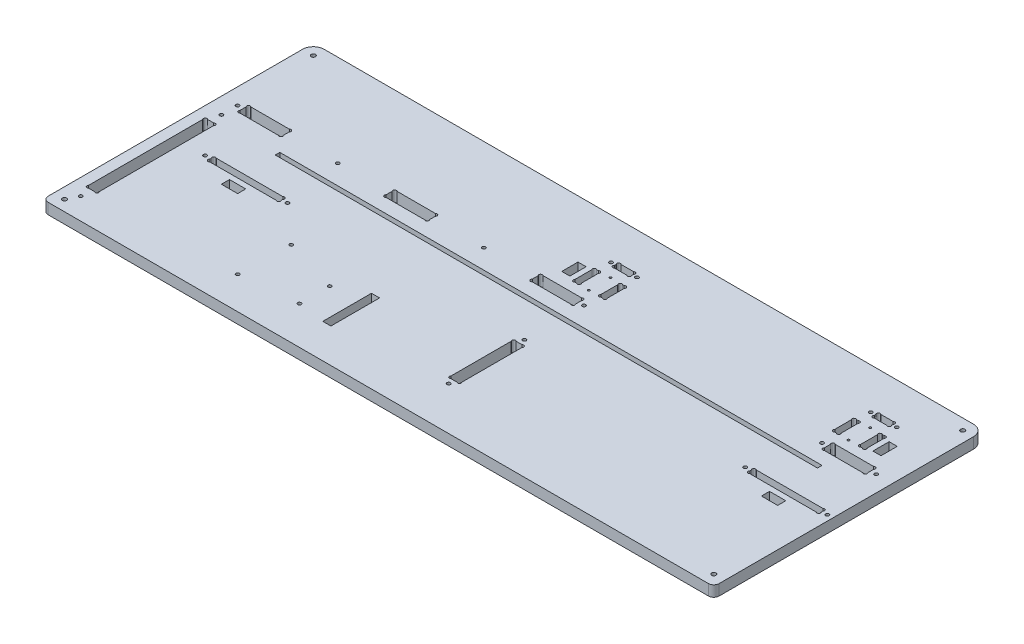
SolidWorks part; units mm, degrees
ref_plane "Plan de face" through (0, 0, 0) normal (0, 0, 1) x (1, 0, 0)
ref_plane "Plan de dessus" through (0, 0, 0) normal (0, 1, 0) x (1, 0, 0)
ref_plane "Plan de droite" through (0, 0, 0) normal (1, 0, 0) x (0, 0, -1)
sketch "Esquisse1" plane through (0, 0, 0) normal (0, 1, 0) x (1, 0, 0)
  line L26 (317, 211.2627) -> (317, 212.7373)
  line L28 (319.2627, 215) -> (330.7373, 215)
  line L29 (333, 211.2627) -> (333, 212.7373)
  line L30 (330.7373, 209) -> (319.2627, 209)
  line L31 (312.2627, 179.5) -> (313.7373, 179.5)
  line L32 (312.2627, 199.5) -> (313.7373, 199.5)
  line L33 (310, 197.2373) -> (310, 181.7627)
  line L34 (316, 181.7627) -> (316, 197.2373)
  line L35 (334, 181.7627) -> (334, 197.2373)
  line L36 (340, 197.2373) -> (340, 181.7627)
  line L37 (337.7373, 199.5) -> (336.2627, 199.5)
  line L38 (337.7373, 179.5) -> (336.2627, 179.5)
  line L39 (552.2627, 179.5) -> (553.7373, 179.5)
  line L40 (552.2627, 199.5) -> (553.7373, 199.5)
  line L41 (550, 197.2373) -> (550, 181.7627)
  line L42 (556, 181.7627) -> (556, 197.2373)
  line L43 (574, 181.7627) -> (574, 197.2373)
  line L44 (580, 197.2373) -> (580, 181.7627)
  line L45 (577.7373, 199.5) -> (576.2627, 199.5)
  line L46 (577.7373, 179.5) -> (576.2627, 179.5)
  line L47 (559.2627, 209) -> (570.7373, 209)
  line L48 (557, 211.2627) -> (557, 212.7373)
  line L49 (570.7373, 215) -> (559.2627, 215)
  line L50 (573, 211.2627) -> (573, 212.7373)
  line L55 (560, 167.7373) -> (560, 162.2627)
  line L56 (600, 167.7373) -> (600, 162.2627)
  line L57 (562.2627, 170) -> (597.7373, 170)
  line L58 (597.7373, 160) -> (562.2627, 160)
  line L59 (292.2627, 160) -> (327.7373, 160)
  line L60 (327.7373, 170) -> (292.2627, 170)
  line L61 (290, 167.7373) -> (290, 162.2627)
  line L62 (330, 167.7373) -> (330, 162.2627)
  line L64 (20, 167.7373) -> (20, 162.2627)
  line L65 (60, 167.7373) -> (60, 162.2627)
  line L66 (22.2627, 170) -> (57.7373, 170)
  line L67 (57.7373, 160) -> (22.2627, 160)
  line L70 (155, 167.7373) -> (155, 162.2627)
  line L71 (195, 167.7373) -> (195, 162.2627)
  line L72 (157.2627, 170) -> (192.7373, 170)
  line L73 (192.7373, 160) -> (157.2627, 160)
  line L76 (10, 250) -> (610, 250)
  line L77 (0, 240) -> (0, 0)
  line L78 (0, 0) -> (620, 0)
  line L79 (620, 240) -> (620, 0)
  line L84 (12.2627, 30) -> (17.7373, 30)
  line L85 (12.2627, 140) -> (17.7373, 140)
  line L86 (10, 137.7373) -> (10, 32.2627)
  line L87 (20, 32.2627) -> (20, 137.7373)
  line L98 (337.7373, 45) -> (332.2627, 45)
  line L99 (337.7373, 105) -> (332.2627, 105)
  line L100 (340, 47.2627) -> (340, 102.7373)
  line L101 (330, 102.7373) -> (330, 47.2627)
  line L109 (610, 109.2627) -> (610, 110.7373)
  line L110 (544, 109.2627) -> (544, 110.7373)
  line L111 (607.7373, 107) -> (546.2627, 107)
  line L112 (546.2627, 113) -> (607.7373, 113)
  line L113 (108.7373, 113) -> (47.2627, 113)
  line L114 (47.2627, 107) -> (108.7373, 107)
  line L115 (111, 109.2627) -> (111, 110.7373)
  line L116 (45, 109.2627) -> (45, 110.7373)
  arc A0 (319.2627, 215) -> (317, 212.7373) centre (318.1314, 213.8686) ccw
  arc A1 (319.2627, 209) -> (317, 211.2627) centre (318.1314, 210.1314) cw
  arc A2 (330.7373, 209) -> (333, 211.2627) centre (331.8686, 210.1314) ccw
  arc A3 (330.7373, 215) -> (333, 212.7373) centre (331.8686, 213.8686) cw
  arc A4 (313.7373, 179.5) -> (316, 181.7627) centre (314.8686, 180.6314) ccw
  arc A5 (312.2627, 179.5) -> (310, 181.7627) centre (311.1314, 180.6314) cw
  arc A6 (312.2627, 199.5) -> (310, 197.2373) centre (311.1314, 198.3686) ccw
  arc A7 (313.7373, 199.5) -> (316, 197.2373) centre (314.8686, 198.3686) cw
  arc A8 (336.2627, 179.5) -> (334, 181.7627) centre (335.1314, 180.6314) cw
  arc A9 (336.2627, 199.5) -> (334, 197.2373) centre (335.1314, 198.3686) ccw
  arc A10 (337.7373, 199.5) -> (340, 197.2373) centre (338.8686, 198.3686) cw
  arc A11 (337.7373, 179.5) -> (340, 181.7627) centre (338.8686, 180.6314) ccw
  arc A12 (552.2627, 179.5) -> (550, 181.7627) centre (551.1314, 180.6314) cw
  arc A13 (552.2627, 199.5) -> (550, 197.2373) centre (551.1314, 198.3686) ccw
  arc A14 (553.7373, 199.5) -> (556, 197.2373) centre (554.8686, 198.3686) cw
  arc A15 (553.7373, 179.5) -> (556, 181.7627) centre (554.8686, 180.6314) ccw
  arc A16 (576.2627, 199.5) -> (574, 197.2373) centre (575.1314, 198.3686) ccw
  arc A17 (577.7373, 199.5) -> (580, 197.2373) centre (578.8686, 198.3686) cw
  arc A18 (577.7373, 179.5) -> (580, 181.7627) centre (578.8686, 180.6314) ccw
  arc A19 (576.2627, 179.5) -> (574, 181.7627) centre (575.1314, 180.6314) cw
  arc A20 (559.2627, 215) -> (557, 212.7373) centre (558.1314, 213.8686) ccw
  arc A21 (559.2627, 209) -> (557, 211.2627) centre (558.1314, 210.1314) cw
  arc A22 (570.7373, 209) -> (573, 211.2627) centre (571.8686, 210.1314) ccw
  arc A23 (570.7373, 215) -> (573, 212.7373) centre (571.8686, 213.8686) cw
  circle A24 centre (313, 212) radius 1.6
  circle A25 centre (337, 212) radius 1.6
  circle A26 centre (553, 212) radius 1.6
  circle A27 centre (577, 212) radius 1.6
  circle A28 centre (555, 165) radius 1.6
  arc A29 (560, 162.2627) -> (562.2627, 160) centre (561.1314, 161.1314) ccw
  arc A30 (560, 167.7373) -> (562.2627, 170) centre (561.1314, 168.8686) cw
  arc A31 (600, 167.7373) -> (597.7373, 170) centre (598.8686, 168.8686) ccw
  arc A32 (600, 162.2627) -> (597.7373, 160) centre (598.8686, 161.1314) cw
  circle A33 centre (605, 165) radius 1.6
  arc A34 (290, 162.2627) -> (292.2627, 160) centre (291.1314, 161.1314) ccw
  arc A35 (290, 167.7373) -> (292.2627, 170) centre (291.1314, 168.8686) cw
  arc A36 (330, 167.7373) -> (327.7373, 170) centre (328.8686, 168.8686) ccw
  arc A37 (330, 162.2627) -> (327.7373, 160) centre (328.8686, 161.1314) cw
  circle A38 centre (335, 165) radius 1.6
  circle A39 centre (15, 165) radius 1.6
  arc A40 (20, 162.2627) -> (22.2627, 160) centre (21.1314, 161.1314) ccw
  arc A41 (20, 167.7373) -> (22.2627, 170) centre (21.1314, 168.8686) cw
  arc A42 (60, 167.7373) -> (57.7373, 170) centre (58.8686, 168.8686) ccw
  arc A43 (60, 162.2627) -> (57.7373, 160) centre (58.8686, 161.1314) cw
  arc A44 (155, 162.2627) -> (157.2627, 160) centre (156.1314, 161.1314) ccw
  arc A45 (155, 167.7373) -> (157.2627, 170) centre (156.1314, 168.8686) cw
  arc A46 (195, 162.2627) -> (192.7373, 160) centre (193.8686, 161.1314) cw
  arc A47 (195, 167.7373) -> (192.7373, 170) centre (193.8686, 168.8686) ccw
  circle A48 centre (242.5, 165) radius 1.6
  circle A49 centre (107.5, 165) radius 1.6
  arc A50 (17.7373, 30) -> (20, 32.2627) centre (18.8686, 31.1314) ccw
  circle A51 centre (15, 20) radius 1.6
  arc A52 (12.2627, 30) -> (10, 32.2627) centre (11.1314, 31.1314) cw
  arc A53 (17.7373, 140) -> (20, 137.7373) centre (18.8686, 138.8686) cw
  arc A54 (12.2627, 140) -> (10, 137.7373) centre (11.1314, 138.8686) ccw
  circle A55 centre (15, 150) radius 1.6
  arc A56 (10, 250) -> (0, 240) centre (10, 240) ccw
  arc A57 (610, 250) -> (620, 240) centre (610, 240) cw
  circle A58 centre (335, 40) radius 1.6
  arc A59 (330, 47.2627) -> (332.2627, 45) centre (331.1314, 46.1314) ccw
  arc A60 (340, 47.2627) -> (337.7373, 45) centre (338.8686, 46.1314) cw
  arc A61 (330, 102.7373) -> (332.2627, 105) centre (331.1314, 103.8686) cw
  arc A62 (340, 102.7373) -> (337.7373, 105) centre (338.8686, 103.8686) ccw
  circle A63 centre (335, 110) radius 1.6
  arc A64 (607.7373, 107) -> (610, 109.2627) centre (608.8686, 108.1314) ccw
  circle A65 centre (615, 110) radius 1.6
  arc A66 (607.7373, 113) -> (610, 110.7373) centre (608.8686, 111.8686) cw
  circle A67 centre (539, 110) radius 1.6
  arc A68 (546.2627, 113) -> (544, 110.7373) centre (545.1314, 111.8686) ccw
  arc A69 (546.2627, 107) -> (544, 109.2627) centre (545.1314, 108.1314) cw
  arc A70 (108.7373, 107) -> (111, 109.2627) centre (109.8686, 108.1314) ccw
  arc A71 (108.7373, 113) -> (111, 110.7373) centre (109.8686, 111.8686) cw
  circle A72 centre (116, 110) radius 1.6
  arc A73 (47.2627, 113) -> (45, 110.7373) centre (46.1314, 111.8686) ccw
  circle A74 centre (40, 110) radius 1.6
  arc A75 (47.2627, 107) -> (45, 109.2627) centre (46.1314, 108.1314) cw
  point P1 (337, 199.5)
  dimension "D25" = 6
  dimension "D28" = 16
  dimension "D29" = 20
  dimension "D32" = 9.5
  dimension "D33" = 35
  dimension "D39" = 10
  dimension "D49" = 1.1314
  dimension "D50" = 40
  dimension "D57" = 6
  dimension "D55" = 76
  dimension "D62" = 3.2
  dimension "D63" = 1.6
  dimension "D64" = 10
  dimension "D65" = 1.1314
  dimension "D66" = 1.1314
  dimension "D67" = 620
  dimension "D9" = 2.2627
  dimension "D10" = 1.6
  dimension "D69" = 3.2
  dimension "D78" = 3.7373
  dimension "D14" = 1.6
  dimension "D36" = 1.6
  dimension "D61" = 1.6
  dimension "D95" = 1.6
  dimension "D107" = 1.6
  dimension "D118" = 1.6
  dimension "D119" = 1.6
  dimension "D128" = 6
  dimension "D141" = 1.6
  dimension "D2" = 250
  dimension "D4" = 5
  dimension "D8" = 20
  dimension "D11" = 5
  dimension "D12" = 5
  dimension "D13" = 40
  dimension "D15" = 5
  dimension "D16" = 1.1314
  dimension "D17" = 1.1314
  dimension "D18" = 5
  dimension "D19" = 2.2627
  dimension "D20" = 2.2627
  dimension "D21" = 80
  dimension "D22" = 10
  dimension "D23" = 1.1314
  dimension "D24" = 1.1314
  dimension "D26" = 6
  dimension "D27" = 6
  dimension "D30" = 40
  dimension "D31" = 18
  dimension "D34" = 4
  dimension "D35" = 4
  dimension "D37" = 1.1314
  dimension "D38" = 2.2627
  dimension "D40" = 1.1314
  dimension "D41" = 1.1314
  dimension "D42" = 1.1314
  dimension "D43" = 1.1314
  dimension "D44" = 3
  dimension "D45" = 1
  dimension "D46" = 1.1314
  dimension "D47" = 1.1314
  dimension "D48" = 1.1314
  dimension "D51" = 3.7373
  dimension "D52" = 66
  dimension "D53" = 10
  dimension "D54" = 66
  dimension "D56" = 107
  dimension "D58" = 3
  dimension "D59" = 1.1314
  dimension "D60" = 2.2627
  dimension "D68" = 60
  dimension "D70" = 6
  dimension "D71" = 3
  dimension "D72" = 1.1314
  dimension "D73" = 1.1314
  dimension "D74" = 63.7373
  dimension "D75" = 2.2627
  dimension "D76" = 2.2627
  dimension "D77" = 45
  dimension "D79" = 45
  dimension "D80" = 5
  dimension "D81" = 5
  dimension "D82" = 5
  dimension "D83" = 280
  dimension "D84" = 1.1314
  dimension "D85" = 1.1314
  dimension "D86" = 1.1314
  dimension "D87" = 1.1314
  dimension "D88" = 10
  dimension "D89" = 110
  dimension "D90" = 30
  dimension "D91" = 10
  dimension "D92" = 5
  dimension "D93" = 10
  dimension "D94" = 10
  dimension "D96" = 1.1314
  dimension "D97" = 1.1314
  dimension "D98" = 1.1314
  dimension "D99" = 92.5
  dimension "D100" = 1.1314
  dimension "D101" = 135
  dimension "D102" = 92.5
  dimension "D103" = 15
  dimension "D104" = 85
  dimension "D105" = 10
  dimension "D106" = 40
  dimension "D108" = 20
  dimension "D109" = 80
  dimension "D110" = 1.1314
  dimension "D111" = 1.1314
  dimension "D112" = 1.1314
  dimension "D113" = 1.1314
  dimension "D114" = 40
  dimension "D115" = 95
  dimension "D116" = 95
  dimension "D117" = 40
  dimension "D120" = 1.1314
  dimension "D121" = 1.1314
  dimension "D122" = 1.1314
  dimension "D123" = 1.1314
  dimension "D124" = 1.1314
  dimension "D125" = 1.1314
  dimension "D126" = 1.1314
  dimension "D127" = 1.1314
  dimension "D129" = 6
  dimension "D130" = 6
  dimension "D131" = 4
  dimension "D132" = 20
  dimension "D133" = 16
  dimension "D134" = 4
  dimension "D135" = 35
  dimension "D136" = 9.5
  dimension "D137" = 283
  dimension "D138" = 3
  dimension "D139" = 1
  dimension "D140" = 18
  dimension "D142" = 1.1314
  dimension "D143" = 1.1314
  dimension "D144" = 1.1314
  dimension "D145" = 1.1314
  dimension "D146" = 1.1314
  dimension "D147" = 1.1314
  dimension "D148" = 1.1314
  dimension "D149" = 1.1314
  dimension "D150" = 1.1314
  dimension "D151" = 1.1314
  dimension "D152" = 1.1314
  dimension "D153" = 1.1314
extrude "Extrusion1" add sketch "Esquisse1" along normal blind 10
sketch "Esquisse2" plane through (0, 10, 0) normal (0, 1, 0) x (-1, 0, 0)
  line L0 (-610, -250) -> (-10, -250) construction
  line L5 (-620, 21.4973) -> (-620, -261.3021) construction
  line L7 (-573, -142.8) -> (-72, -142.8)
  line L8 (-573, -142.8) -> (-573, -147)
  line L9 (-573, -147) -> (-72, -147)
  line L10 (-72, -142.8) -> (-72, -147)
  dimension "D1" = 47
  dimension "D2" = 4.2
  dimension "D3" = 501
  dimension "D4" = 103
extrude "Enlèv. mat.-Extru.1" cut sketch "Esquisse2" against normal through all
sketch "Esquisse3" plane through (0, 10, 0) normal (0, 1, 0) x (1, 0, 0)
  line L0 (574, 197.2373) -> (574, 181.7627) construction
  line L1 (556, 181.7627) -> (556, 197.2373) construction
  line L2 (559.2627, 209) -> (570.7373, 209) construction
  line L4 (576.2627, 179.5) -> (577.7373, 179.5) construction
  line L5 (577.7373, 199.5) -> (576.2627, 199.5) construction
  line L6 (334, 197.2373) -> (334, 181.7627) construction
  circle A0 centre (565, 179.5) radius 1
  circle A1 centre (565, 199.5) radius 1
  circle A2 centre (325, 179.5) radius 1
  circle A3 centre (325, 199.5) radius 1
  dimension "D1" = 2
  dimension "D2" = 9
  dimension "D3" = 9
  dimension "D4" = 20
  dimension "D5" = 9.5
  dimension "D6" = 0
  dimension "D7" = 0
  dimension "D8" = 9
extrude "Enlèv. mat.-Extru.2" cut sketch "Esquisse3" against normal through all
fillet "Congé1" radius 5 2 edges at (620, 5, 0) (0, 5, 0)
sketch "Esquisse4" plane through (0, 0, 0) normal (0, -1, 0) x (1, 0, 0)
  line L0 (0, -240) -> (0, -5) construction
  line L1 (5, 0) -> (615, 0) construction
  line L2 (610, -250) -> (10, -250) construction
  line L3 (620, -5) -> (620, -240) construction
  circle A0 centre (10, -10) radius 2
  circle A1 centre (610, -10) radius 2
  circle A2 centre (610, -240) radius 2
  circle A3 centre (10, -240) radius 2
  dimension "D1" = 4
  dimension "D2" = 10
  dimension "D3" = 10
  dimension "D4" = 10
  dimension "D5" = 10
  dimension "D6" = 10
  dimension "D7" = 10
  dimension "D8" = 10
  dimension "D9" = 10
extrude "Enlèv. mat.-Extru.3" cut sketch "Esquisse4" against normal through all
sketch "Esquisse5" plane through (0, 10, 0) normal (0, 1, 0) x (1, 0, 0)
  line L1 (0, 240) -> (0, 5) construction
  line L2 (5, 0) -> (615, 0) construction
  circle A0 centre (151.27, 78.26) radius 1.59
  circle A1 centre (150, 30) radius 1.59
  circle A2 centre (202.07, 63.02) radius 1.59
  circle A3 centre (202.07, 35.08) radius 1.59
  point P8 (150, 78.4116)
  point P9 (156.1886, 76.9743)
  dimension "D1" = 3.18
  dimension "D7" = 30
  dimension "D2" = 48.26
  dimension "D3" = 27.94
  dimension "D4" = 52.07
  dimension "D5" = 5.08
  dimension "D6" = 150
  dimension "D8" = 1.27
extrude "Enlèv. mat.-Extru.4" cut sketch "Esquisse5" against normal through all
sketch "Esquisse6" plane through (0, 10, 0) normal (0, 1, 0) x (1, 0, 0)
  line L0 (544, 110.7373) -> (544, 109.2627) construction
  line L1 (569.5, 102) -> (584.5, 102)
  line L2 (569.5, 102) -> (569.5, 94.5)
  line L3 (569.5, 94.5) -> (584.5, 94.5)
  line L4 (584.5, 102) -> (584.5, 94.5)
  line L5 (610, 109.2627) -> (610, 110.7373) construction
  line L6 (546.2627, 107) -> (607.7373, 107) construction
  line L8 (585, 197) -> (592.5, 197)
  line L9 (585, 197) -> (585, 182)
  line L10 (585, 182) -> (592.5, 182)
  line L11 (592.5, 197) -> (592.5, 182)
  line L12 (305, 197) -> (297.5, 197)
  line L13 (305, 197) -> (305, 182)
  line L14 (305, 182) -> (297.5, 182)
  line L15 (297.5, 197) -> (297.5, 182)
  line L16 (577.7373, 199.5) -> (576.2627, 199.5) construction
  line L17 (576.2627, 179.5) -> (577.7373, 179.5) construction
  line L18 (580, 181.7627) -> (580, 197.2373) construction
  line L19 (310, 197.2373) -> (310, 181.7627) construction
  line L20 (313.7373, 199.5) -> (312.2627, 199.5) construction
  line L21 (45, 110.7373) -> (45, 109.2627) construction
  line L22 (227.07, 76.63) -> (234.57, 76.63)
  line L23 (227.07, 76.63) -> (227.07, 31.63)
  line L24 (227.07, 31.63) -> (234.57, 31.63)
  line L25 (234.57, 76.63) -> (234.57, 31.63)
  line L26 (70.5, 102) -> (85.5, 102)
  line L27 (70.5, 102) -> (70.5, 94.5)
  line L28 (70.5, 94.5) -> (85.5, 94.5)
  line L29 (85.5, 102) -> (85.5, 94.5)
  circle A0 centre (150, 30) radius 1.59 construction
  circle A1 centre (151.27, 78.26) radius 1.59 construction
  circle A2 centre (202.07, 63.02) radius 1.59 construction
  dimension "D1" = 15
  dimension "D2" = 7.5
  dimension "D3" = 25.5
  dimension "D4" = 25.5
  dimension "D5" = 5
  dimension "D6" = 7.5
  dimension "D7" = 15
  dimension "D8" = 15
  dimension "D9" = 7.5
  dimension "D10" = 2.5
  dimension "D11" = 2.5
  dimension "D12" = 5
  dimension "D13" = 5
  dimension "D14" = 2.5
  dimension "D15" = 7.5
  dimension "D16" = 45
  dimension "D17" = 1.63
  dimension "D18" = 1.63
  dimension "D19" = 25
  dimension "D20" = 15
  dimension "D21" = 25.5
extrude "Enlèv. mat.-Extru.5" cut sketch "Esquisse6" against normal through all
